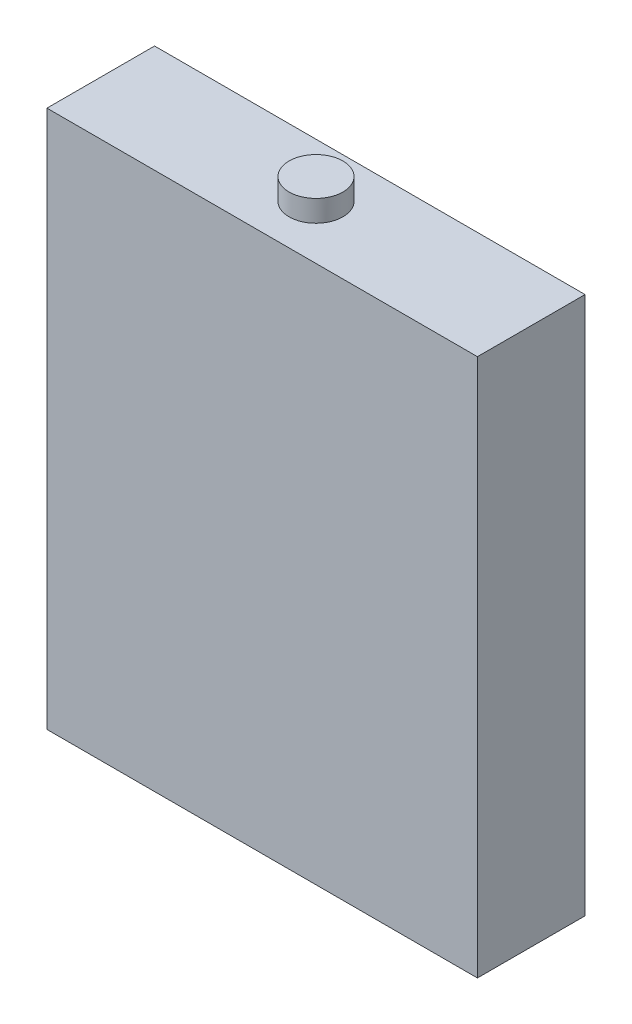
SolidWorks part; units mm, degrees
ref_plane "Front Plane" through (0, 0, 0) normal (0, 0, 1) x (1, 0, 0)
ref_plane "Top Plane" through (0, 0, 0) normal (0, 1, 0) x (1, 0, 0)
ref_plane "Right Plane" through (0, 0, 0) normal (1, 0, 0) x (0, 0, -1)
sketch "Sketch2" plane through (0, 0, 0) normal (0, 1, 0) x (1, 0, 0)
  line L1 (-20, -5) -> (20, -5)
  line L2 (-20, -5) -> (-20, 5)
  line L3 (-20, 5) -> (20, 5)
  line L4 (20, -5) -> (20, 5)
  line L5 (-20, -5) -> (20, 5) construction
  line L6 (-20, 5) -> (20, -5) construction
  point P0 (0, 0)
  dimension "D1" = 10
  dimension "D2" = 40
extrude "Boss-Extrude1" add sketch "Sketch2" along normal blind 50
sketch "Sketch3" plane through (0, 50, 0) normal (0, 1, 0) x (1, 0, 0)
  circle A0 centre (0, 0) radius 2.5
  dimension "D1" = 5
extrude "Boss-Extrude2" add sketch "Sketch3" along normal blind 2
